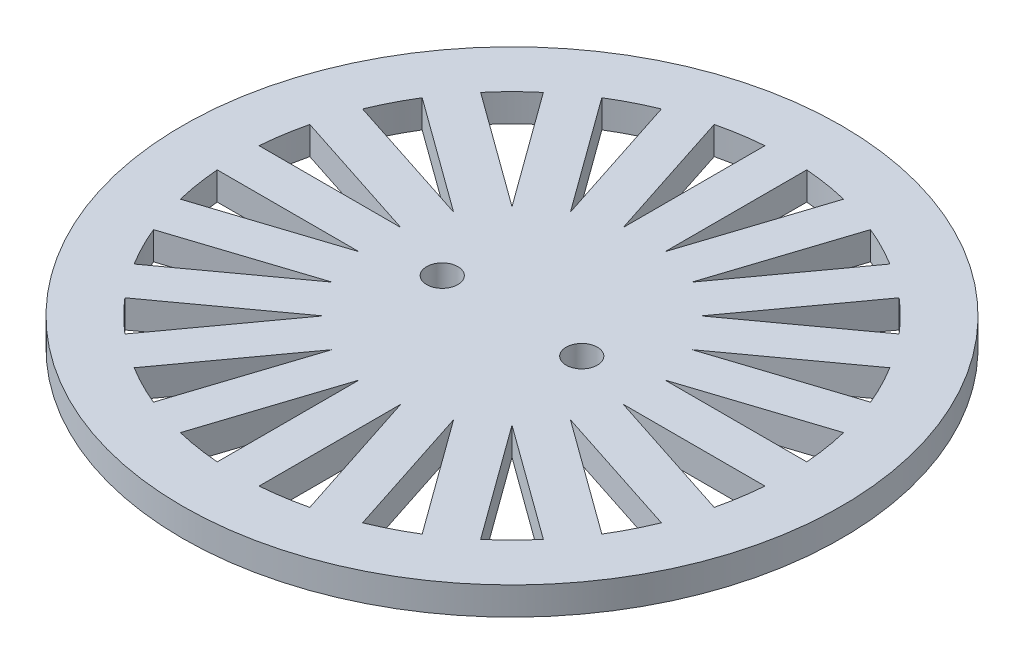
SolidWorks part; units mm, degrees
ref_plane "Front Plane" through (0, 0, 0) normal (0, 0, 1) x (1, 0, 0)
ref_plane "Top Plane" through (0, 0, 0) normal (0, 1, 0) x (1, 0, 0)
ref_plane "Right Plane" through (0, 0, 0) normal (1, 0, 0) x (0, 0, -1)
sketch "Sketch1" plane through (0, 0, 0) normal (0, 1, 0) x (1, 0, 0)
  line L0 (-1.905, 24.9273) -> (-1.905, 12.0277)
  line L1 (1.905, 24.9273) -> (1.905, 12.0277)
  line L2 (5.8912, 24.296) -> (1.905, 12.0277)
  line L3 (9.5147, 23.1186) -> (5.5285, 10.8503)
  line L4 (13.1107, 21.2864) -> (5.5285, 10.8503)
  line L5 (16.1931, 19.0469) -> (8.6109, 8.6109)
  line L6 (19.0469, 16.1931) -> (8.6109, 8.6109)
  line L7 (21.2864, 13.1107) -> (10.8503, 5.5285)
  line L8 (23.1186, 9.5147) -> (10.8503, 5.5285)
  line L9 (24.296, 5.8912) -> (12.0277, 1.905)
  line L10 (24.9273, 1.905) -> (12.0277, 1.905)
  line L11 (24.9273, -1.905) -> (12.0277, -1.905)
  line L12 (24.296, -5.8912) -> (12.0277, -1.905)
  line L13 (23.1186, -9.5147) -> (10.8503, -5.5285)
  line L14 (21.2864, -13.1107) -> (10.8503, -5.5285)
  line L15 (19.0469, -16.1931) -> (8.6109, -8.6109)
  line L16 (16.1931, -19.0469) -> (8.6109, -8.6109)
  line L17 (13.1107, -21.2864) -> (5.5285, -10.8503)
  line L18 (9.5147, -23.1186) -> (5.5285, -10.8503)
  line L19 (5.8912, -24.296) -> (1.905, -12.0277)
  line L20 (1.905, -24.9273) -> (1.905, -12.0277)
  line L21 (-1.905, -24.9273) -> (-1.905, -12.0277)
  line L22 (-5.8912, -24.296) -> (-1.905, -12.0277)
  line L23 (-9.5147, -23.1186) -> (-5.5285, -10.8503)
  line L24 (-13.1107, -21.2864) -> (-5.5285, -10.8503)
  line L25 (-16.1931, -19.0469) -> (-8.6109, -8.6109)
  line L26 (-19.0469, -16.1931) -> (-8.6109, -8.6109)
  line L27 (-21.2864, -13.1107) -> (-10.8503, -5.5285)
  line L28 (-23.1186, -9.5147) -> (-10.8503, -5.5285)
  line L29 (-24.296, -5.8912) -> (-12.0277, -1.905)
  line L30 (-24.9273, -1.905) -> (-12.0277, -1.905)
  line L31 (-24.9273, 1.905) -> (-12.0277, 1.905)
  line L32 (-24.296, 5.8912) -> (-12.0277, 1.905)
  line L33 (-23.1186, 9.5147) -> (-10.8503, 5.5285)
  line L34 (-21.2864, 13.1107) -> (-10.8503, 5.5285)
  line L35 (-19.0469, 16.1931) -> (-8.6109, 8.6109)
  line L36 (-16.1931, 19.0469) -> (-8.6109, 8.6109)
  line L37 (-13.1107, 21.2864) -> (-5.5285, 10.8503)
  line L38 (-9.5147, 23.1186) -> (-5.5285, 10.8503)
  line L39 (-5.8912, 24.296) -> (-1.905, 12.0277)
  circle A0 centre (0, 0) radius 30
  arc A1 (-9.5147, 23.1186) -> (-13.1107, 21.2864) centre (0, 0) ccw
  circle A2 centre (0, 0) radius 11.1806
  circle A3 centre (6.35, 0) radius 1.4224
  circle A4 centre (-6.35, 0) radius 1.4224
  arc A5 (-16.1931, 19.0469) -> (-19.0469, 16.1931) centre (0, 0) ccw
  arc A6 (-21.2864, 13.1107) -> (-23.1186, 9.5147) centre (0, 0) ccw
  arc A7 (-1.905, 24.9273) -> (-5.8912, 24.296) centre (0, 0) ccw
  arc A8 (5.8912, 24.296) -> (1.905, 24.9273) centre (0, 0) ccw
  arc A9 (13.1107, 21.2864) -> (9.5147, 23.1186) centre (0, 0) ccw
  arc A10 (19.0469, 16.1931) -> (16.1931, 19.0469) centre (0, 0) ccw
  arc A11 (23.1186, 9.5147) -> (21.2864, 13.1107) centre (0, 0) ccw
  arc A12 (24.9273, 1.905) -> (24.296, 5.8912) centre (0, 0) ccw
  arc A13 (-24.296, 5.8912) -> (-24.9273, 1.905) centre (0, 0) ccw
  arc A14 (-24.9273, -1.905) -> (-24.296, -5.8912) centre (0, 0) ccw
  arc A15 (-23.1186, -9.5147) -> (-21.2864, -13.1107) centre (0, 0) ccw
  arc A16 (-19.0469, -16.1931) -> (-16.1931, -19.0469) centre (0, 0) ccw
  arc A17 (-13.1107, -21.2864) -> (-9.5147, -23.1186) centre (0, 0) ccw
  arc A18 (-5.8912, -24.296) -> (-1.905, -24.9273) centre (0, 0) ccw
  arc A19 (1.905, -24.9273) -> (5.8912, -24.296) centre (0, 0) ccw
  arc A20 (9.5147, -23.1186) -> (13.1107, -21.2864) centre (0, 0) ccw
  arc A21 (16.1931, -19.0469) -> (19.0469, -16.1931) centre (0, 0) ccw
  arc A22 (21.2864, -13.1107) -> (23.1186, -9.5147) centre (0, 0) ccw
  arc A23 (24.296, -5.8912) -> (24.9273, -1.905) centre (0, 0) ccw
  point P92 (0, 0)
  dimension "D1" = 6.35
  dimension "D3" = 2.8448
  dimension "D4" = 2.8448
  dimension "D5" = 1.905
  dimension "D8" = 60
  dimension "D9" = 25
  dimension "D2" = 6.35
  dimension "D6" = 1.905
  dimension "D7" = 20
extrude "Boss-Extrude1" add sketch "Sketch1" along normal blind 2.54 contours A0 A23 L12 L11 A22 L14 L13 A21 L16 L15 A20 L18 L17 A19 L20 L19 A18 L22 L21 A17 L24 L23 A16 L26 L25 A15 L28 L27 A14 L30 L29 A13 L32 L31 A12 L10 L9 A11 | A2 A4 A3
